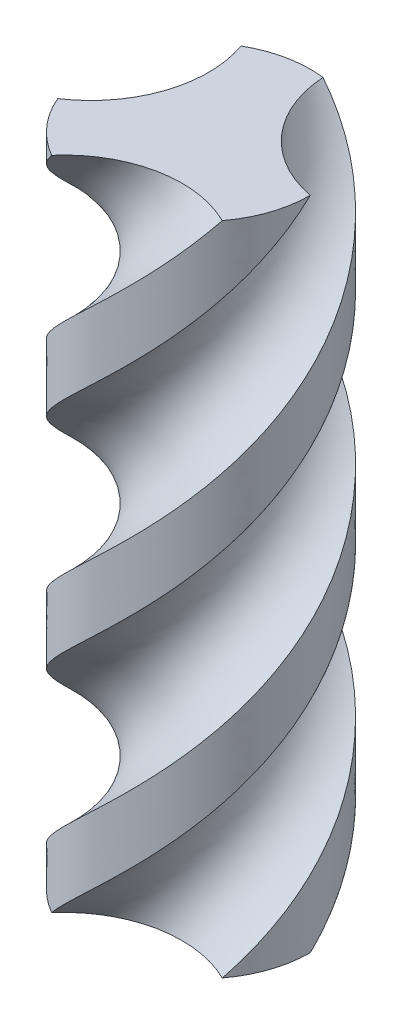
SolidWorks part; units mm, degrees
ref_plane "Front Plane" through (0, 0, 0) normal (0, 0, 1) x (1, 0, 0)
ref_plane "Top Plane" through (0, 0, 0) normal (0, 1, 0) x (1, 0, 0)
ref_plane "Right Plane" through (0, 0, 0) normal (1, 0, 0) x (0, 0, -1)
sketch "Sketch2" plane through (0, 0, 0) normal (0, 1, 0) x (1, 0, 0)
  line L0 (-25, 43.3013) -> (0, 0)
  line L1 (0, 0) -> (50, -0.0014)
  arc A0 (6.1941, 49.6148) -> (-25, 43.3013) centre (0, 0) ccw
  arc A1 (50, -0.0014) -> (6.1941, 49.6148) centre (59.9709, 52.948) cw
  point P1 (39.2072, 31.029)
  dimension "D4" = 50
  dimension "D5" = 80
  dimension "D6" = 120
  dimension "D13" = 31.8266
  dimension "D2" = 50
  dimension "D3" = 53.88
sketch "Sketch4" plane through (0, 0, 0) normal (0, 1, 0) x (1, 0, 0)
  circle A0 centre (0, 0) radius 50
  dimension "D1" = 100
curve "Helix/Spiral2" pitch 300 height 300 turns 1
sweep "Sweep3" add profiles "Sketch2" path "Helix/Spiral2"
pattern_circular "CirPattern1" count 3 over 360 about axis through (0, 0, 0) along (0, 1, 0) of "Sweep3"
